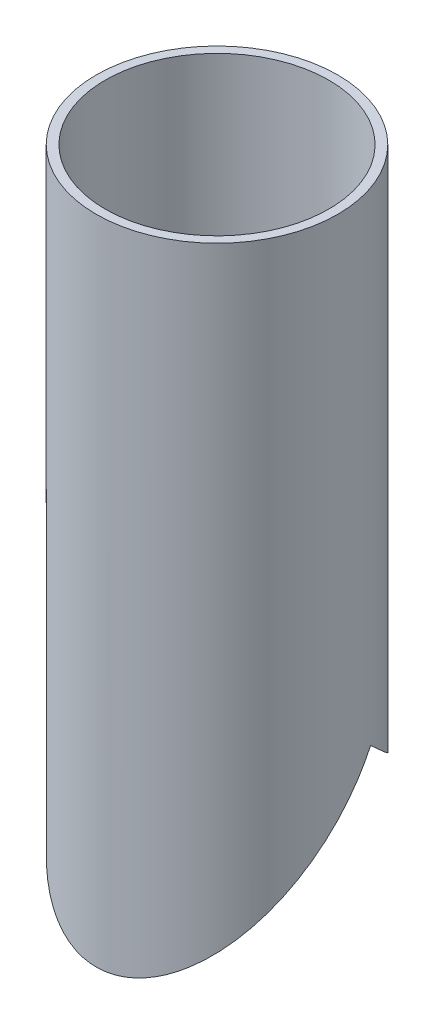
SolidWorks part; units mm, degrees
ref_plane "Front" through (0, 0, 0) normal (0, 0, 1) x (1, 0, 0)
ref_plane "Top" through (0, 0, 0) normal (0, 1, 0) x (1, 0, 0)
ref_plane "Right" through (0, 0, 0) normal (1, 0, 0) x (0, 0, -1)
sketch "Sketch1" plane through (0, 0, 0) normal (1, 0, 0) x (0, 0, -1)
  line L0 (0, 0) -> (0, 36.9644) construction
  line L1 (20.574, 0) -> (20.574, 120.65)
  line L2 (20.574, 120.65) -> (22.225, 120.65)
  line L3 (22.225, 120.65) -> (22.225, 0)
  line L4 (22.225, 0) -> (20.574, 0)
  dimension "D1" = 120.65
  dimension "D2" = 1.651
  dimension "D3" = 20.574
revolve "Revolve1" add sketch "Sketch1" angle 360 about L0
ref_plane "Plane1" through (2.54, 0, 0) normal (1, 0, 0) x (0, 0, -1)
sketch "Sketch3" plane through (2.54, 0, 0) normal (1, 0, 0) x (0, 0, -1)
  line L0 (22.225, 17.5578) -> (22.225, 0)
  line L3 (22.225, 0) -> (22.225, 120.65) construction
  line L4 (22.225, 0) -> (-22.225, 0)
  line L6 (-22.225, 0) -> (-22.225, 0.6737)
  line L12 (7.2738, 31.75) -> (22.225, 17.5578)
  line L13 (-22.225, 0.6737) -> (7.2738, 31.75)
  point P15 (-21.463, 120.65)
  point P16 (-21.463, 1.5875)
  dimension "D1" = 20.6145
  dimension "D2" = 42.8476
  dimension "D3" = 46.492
  dimension "D4" = 31.75
  dimension "D5" = 14.9512
extrude "Cut-Extrude1" cut sketch "Sketch3" against normal through all and the other way through all
